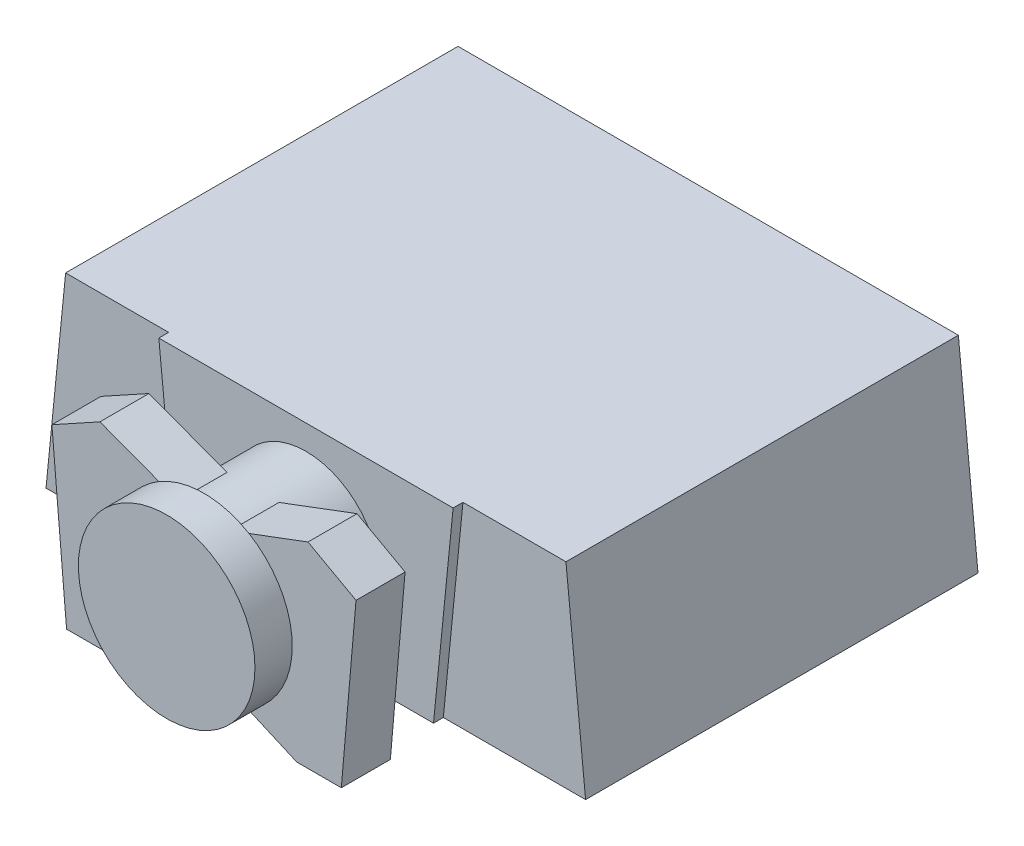
SolidWorks part; units mm, degrees
ref_plane "Front Plane" through (0, 0, 0) normal (0, 0, 1) x (1, 0, 0)
ref_plane "Top Plane" through (0, 0, 0) normal (0, 1, 0) x (1, 0, 0)
ref_plane "Right Plane" through (0, 0, 0) normal (1, 0, 0) x (0, 0, -1)
sketch "Sketch1" plane through (0, 0, 0) normal (0, 0, 1) x (1, 0, 0)
  line L0 (0, 103.326) -> (0, -86.038) construction
  line L1 (-137.5, -50) -> (-127.5, 50)
  line L2 (-137.5, 50) -> (137.5, 50)
  line L3 (-137.5, 50) -> (-137.5, -50)
  line L4 (-137.5, -50) -> (137.5, -50)
  line L5 (137.5, 50) -> (137.5, -50)
  line L6 (-137.5, 50) -> (137.5, -50) construction
  line L7 (-137.5, -50) -> (137.5, 50) construction
  line L8 (137.5, -50) -> (127.5, 50)
  point P1 (0, 0)
  dimension "D1" = 275
  dimension "D2" = 255
  dimension "D3" = 100
extrude "Boss-Extrude1" add sketch "Sketch1" against normal blind 200 contours L4 L8 L2 L1
sketch "Sketch2" plane through (0, 0, 0) normal (0, 0, -1) x (-1, 0, 0)
  line L0 (-75, 50) -> (-65, -50)
  line L1 (127.5, 50) -> (-127.5, 50) construction
  line L2 (137.5, -50) -> (-137.5, -50) construction
  line L3 (137.5, -50) -> (127.5, 50) construction
  line L4 (0, 50) -> (0, -50) construction
  line L5 (75, 50) -> (65, -50)
  line L6 (-75, 50) -> (75, 50)
  line L7 (-65, -50) -> (65, -50)
  dimension "D1" = 150
extrude "Boss-Extrude2" add sketch "Sketch2" against normal blind 5
sketch "Sketch3" plane through (0, 0, 5) normal (0, 0, 1) x (1, 0, 0)
  circle A0 centre (0, 0) radius 37.5
  dimension "D1" = 75
extrude "Boss-Extrude3" add sketch "Sketch3" along normal blind 27
sketch "Sketch4" plane through (0, 0, 32) normal (0, 0, 1) x (1, 0, 0)
  line L0 (-13.2636, 35.076) -> (-53.0235, 50)
  line L1 (77.5, 50) -> (-77.5, 50)
  line L2 (77.5, 50) -> (77.5, -50)
  line L3 (77.5, -50) -> (-77.5, -50)
  line L4 (-77.5, 50) -> (-77.5, -50)
  line L5 (77.5, 50) -> (-77.5, -50) construction
  line L6 (77.5, -50) -> (-77.5, 50) construction
  line L7 (-53.0235, 50) -> (-77.5, 36.4921)
  line L8 (-77.5, 36.4921) -> (-70.0156, -50)
  line L9 (-70.0156, -50) -> (-47.2913, -50)
  line L10 (-47.2913, -50) -> (-13.2636, -35.076)
  line L11 (0, 50) -> (0, -50) construction
  line L12 (47.2913, -50) -> (13.2636, -35.076)
  line L13 (77.5, 36.4921) -> (70.0156, -50)
  line L14 (53.0235, 50) -> (77.5, 36.4921)
  line L15 (13.2636, 35.076) -> (53.0235, 50)
  circle A0 centre (0, 0) radius 37.5 construction
  circle A1 centre (0, 0) radius 37.5
  point P0 (0, 0)
  circle M5 centre (0, 0) radius 37.5
  dimension "D1" = 155
  dimension "D2" = 100
extrude "Boss-Extrude4" add sketch "Sketch4" along normal blind 25 contours L3 L10 L0 L7 L8 M5 | M5 | L15 L12 L3 L13 L14 M5
sketch "Sketch5" plane through (0, 0, 57) normal (0, 0, 1) x (1, 0, 0)
  circle A0 centre (0, 0) radius 45
  dimension "D1" = 90
extrude "Boss-Extrude5" add sketch "Sketch5" along normal blind 19
